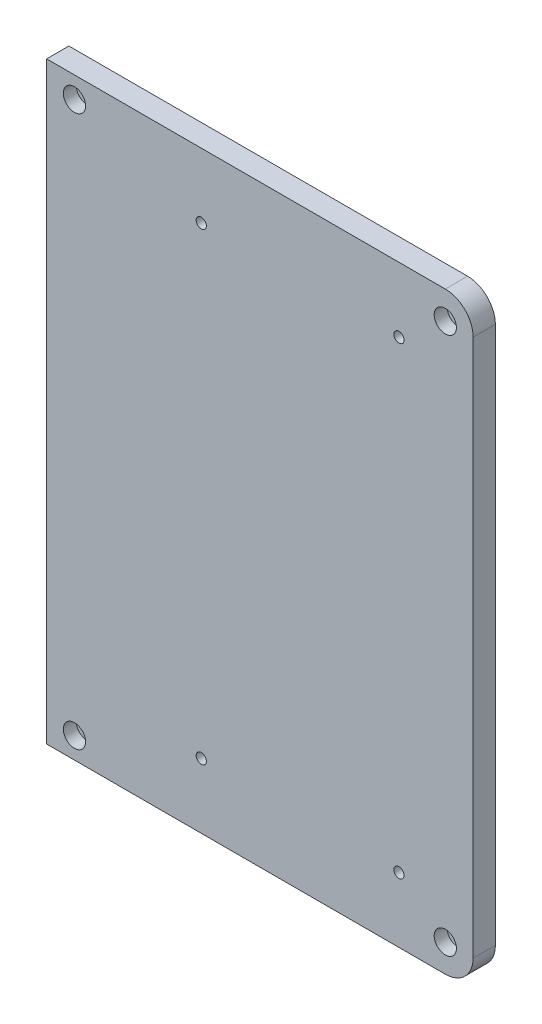
SolidWorks part; units mm, degrees
ref_plane "Front Plane" through (0, 0, 0) normal (0, 0, 1) x (1, 0, 0)
ref_plane "Top Plane" through (0, 0, 0) normal (0, 1, 0) x (1, 0, 0)
ref_plane "Right Plane" through (0, 0, 0) normal (1, 0, 0) x (0, 0, -1)
sketch "Sketch1" plane through (0, 0, 0) normal (0, 0, 1) x (1, 0, 0)
  line L1 (-107.5, 80) -> (107.5, 80)
  line L2 (-115, 72.5) -> (-115, -72.5)
  line L3 (-107.5, -80) -> (107.5, -80)
  line L4 (115, 72.5) -> (115, -72.5)
  line L5 (-115, 80) -> (115, -80) construction
  line L6 (-115, -80) -> (115, 80) construction
  arc A0 (-115, -72.5) -> (-107.5, -80) centre (-107.5, -72.5) ccw
  arc A1 (107.5, -80) -> (115, -72.5) centre (107.5, -72.5) ccw
  arc A2 (107.5, 80) -> (115, 72.5) centre (107.5, 72.5) cw
  arc A3 (-107.5, 80) -> (-115, 72.5) centre (-107.5, 72.5) ccw
  point P0 (0, 0)
  dimension "D3" = 7.5
  dimension "D1" = 230
  dimension "D2" = 160
extrude "Boss-Extrude1" add sketch "Sketch1" along normal blind 6
sketch "Sketch2" plane through (0, 0, 6) normal (0, 0, 1) x (1, 0, 0)
  line L0 (-115, 72.5) -> (-115, -72.5) construction
  line L1 (-107.5, -80) -> (107.5, -80) construction
  line L2 (107.5, 80) -> (-107.5, 80) construction
  line L3 (115, -72.5) -> (115, 72.5) construction
  circle A0 centre (-107.5, -72.5) radius 1.75
  circle A1 centre (-107.5, 72.5) radius 1.75
  circle A2 centre (107.5, -72.5) radius 1.75
  circle A3 centre (107.5, 72.5) radius 1.75
  dimension "D1" = 7.5
  dimension "D3" = 3.5
  dimension "D4" = 3.5
  dimension "D7" = 3.5
  dimension "D10" = 3.5
  dimension "D2" = 7.5
  dimension "D5" = 7.5
  dimension "D6" = 7.5
  dimension "D8" = 7.5
  dimension "D9" = 7.5
  dimension "D11" = 7.5
  dimension "D12" = 7.5
extrude "Cut-Extrude1" cut sketch "Sketch2" against normal blind 10
sketch "Sketch3" plane through (0, 0, 6) normal (0, 0, 1) x (1, 0, 0)
  circle A0 centre (-107.5, -72.5) radius 3
  circle A1 centre (-107.5, 72.5) radius 3
  circle A2 centre (107.5, 72.5) radius 3
  circle A3 centre (107.5, -72.5) radius 3
  dimension "D1" = 6
  dimension "D2" = 6
  dimension "D3" = 6
  dimension "D4" = 6
extrude "Cut-Extrude2" cut sketch "Sketch3" against normal blind 3.5
sketch "Sketch4" plane through (0, 0, 6) normal (0, 0, 1) x (1, 0, 0)
  line L0 (107.5, 80) -> (-107.5, 80) construction
  line L3 (-115, 72.5) -> (-115, -72.5) construction
  line L4 (-107.5, -80) -> (107.5, -80) construction
  circle A0 centre (-96.5, 37.5) radius 1.5
  circle A1 centre (-96.5, -37.5) radius 1.5
  circle A2 centre (-24.5, 37.5) radius 1.5
  circle A3 centre (-24.5, -37.5) radius 1.5
  dimension "D2" = 3
  dimension "D3" = 3
  dimension "D6" = 3
  dimension "D7" = 3
  dimension "D1" = 75
  dimension "D4" = 42.5
  dimension "D5" = 18.5
  dimension "D8" = 72
  dimension "D9" = 72
  dimension "D10" = 42.5
  dimension "D11" = 42.5
extrude "Cut-Extrude3" cut sketch "Sketch4" against normal through all
sketch "Sketch5" plane through (0, 0, 6) normal (0, 0, 1) x (1, 0, 0)
  line L0 (-107.5, -80) -> (107.5, -80) construction
  line L2 (115, -72.5) -> (115, 72.5) construction
  circle A0 centre (95, -62.5) radius 1.375
  circle A1 centre (95, 62.5) radius 1.375
  circle A2 centre (41.7, -62.5) radius 1.375
  circle A3 centre (41.7, 62.5) radius 1.375
  dimension "D1" = 125
  dimension "D4" = 2.75
  dimension "D6" = 53.3
  dimension "D2" = 17.5
  dimension "D3" = 20
  dimension "D5" = 53.3
extrude "Cut-Extrude4" cut sketch "Sketch5" against normal through all and the other way through all
sketch "Sketch7" plane through (0, 0, 6) normal (0, 0, 1) x (1, 0, 0)
  circle A0 centre (-102.8, 42.3) radius 1.5
  circle A1 centre (-96.5, 37.5) radius 1.5 construction
  circle A2 centre (-102.8, -42.3) radius 1.5
  circle A3 centre (-18.2, -42.3) radius 1.5
  circle A4 centre (-18.2, 42.3) radius 1.5
  circle A5 centre (-96.5, -37.5) radius 1.5 construction
  circle A6 centre (-24.5, -37.5) radius 1.5 construction
  circle A7 centre (-24.5, 37.5) radius 1.5 construction
  dimension "D1" = 6.3
  dimension "D3" = 3
  dimension "D4" = 3
  dimension "D5" = 3
  dimension "D6" = 3
  dimension "D7" = 4.8
  dimension "D8" = 6.3
  dimension "D10" = 4.8
  dimension "D11" = 4.8
  dimension "D12" = 6.3
  dimension "D2" = 4.8
extrude "Cut-Extrude6" cut sketch "Sketch7" against normal through all
sketch "Sketch8" plane through (0, 0, 0) normal (0, 0, -1) x (-1, 0, 0)
  circle A0 centre (18.2, 42.3) radius 3
  circle A1 centre (18.2, -42.3) radius 3
  circle A2 centre (102.8, -42.3) radius 3
  circle A3 centre (102.8, 42.3) radius 3
  dimension "D1" = 6
  dimension "D2" = 6
  dimension "D3" = 6
  dimension "D4" = 6
extrude "Cut-Extrude7" cut sketch "Sketch8" against normal blind 3.5
sketch "Sketch9" plane through (0, 0, 6) normal (0, 0, 1) x (1, 0, 0)
  line L0 (115, -72.5) -> (115, 72.5) construction
  line L1 (-115, 80) -> (0, 80)
  line L2 (-115, 80) -> (-115, -80)
  line L3 (-115, -80) -> (0, -80)
  line L4 (0, 80) -> (0, -80)
  line L5 (107.5, 80) -> (-107.5, 80) construction
  line L6 (-107.5, -80) -> (107.5, -80) construction
  line L7 (-115, 72.5) -> (-115, -72.5) construction
  dimension "D1" = 115
  dimension "D2" = 0
  dimension "D3" = 0
  dimension "D4" = 0
extrude "Cut-Extrude8" cut sketch "Sketch9" against normal blind 10
sketch "Sketch10" plane through (0, 0, 6) normal (0, 0, 1) x (1, 0, 0)
  line L1 (0, -80) -> (107.5, -80) construction
  line L2 (0, -80) -> (0, 80) construction
  circle A0 centre (7.5, -74.25) radius 1.75
  dimension "D1" = 3.5
  dimension "D2" = 7.5
  dimension "D3" = 5.75
extrude "Cut-Extrude9" cut sketch "Sketch10" against normal up to surface (6 mm away) up to face at (96.375, 62.5, 0)
sketch "Sketch14" plane through (0, 0, 6) normal (0, 0, 1) x (1, 0, 0)
  line L1 (0, -80) -> (107.5, -80) construction
  line L2 (0, -80) -> (0, 80) construction
  circle A0 centre (7.5, -74.25) radius 3
  dimension "D3" = 6
  dimension "D1" = 7.5
  dimension "D2" = 5.75
extrude "Cut-Extrude10" cut sketch "Sketch14" against normal blind 3.5
sketch "Sketch16" plane through (0, 0, 6) normal (0, 0, 1) x (1, 0, 0)
  line L0 (107.5, 80) -> (0, 80) construction
  line L2 (0, -80) -> (0, 80) construction
  circle A0 centre (7.5, 74.25) radius 1.75
  dimension "D3" = 3.5
  dimension "D1" = 5.75
  dimension "D2" = 7.5
extrude "Cut-Extrude11" cut sketch "Sketch16" against normal up to surface (6 mm away) up to face at (9.25, -74.25, 0)
sketch "Sketch17" plane through (0, 0, 6) normal (0, 0, 1) x (1, 0, 0)
  line L0 (107.5, 80) -> (0, 80) construction
  line L2 (0, -80) -> (0, 80) construction
  circle A0 centre (7.5, 74.25) radius 3
  dimension "D1" = 6
  dimension "D2" = 5.75
  dimension "D3" = 7.5
extrude "Cut-Extrude12" cut sketch "Sketch17" against normal blind 3.5
